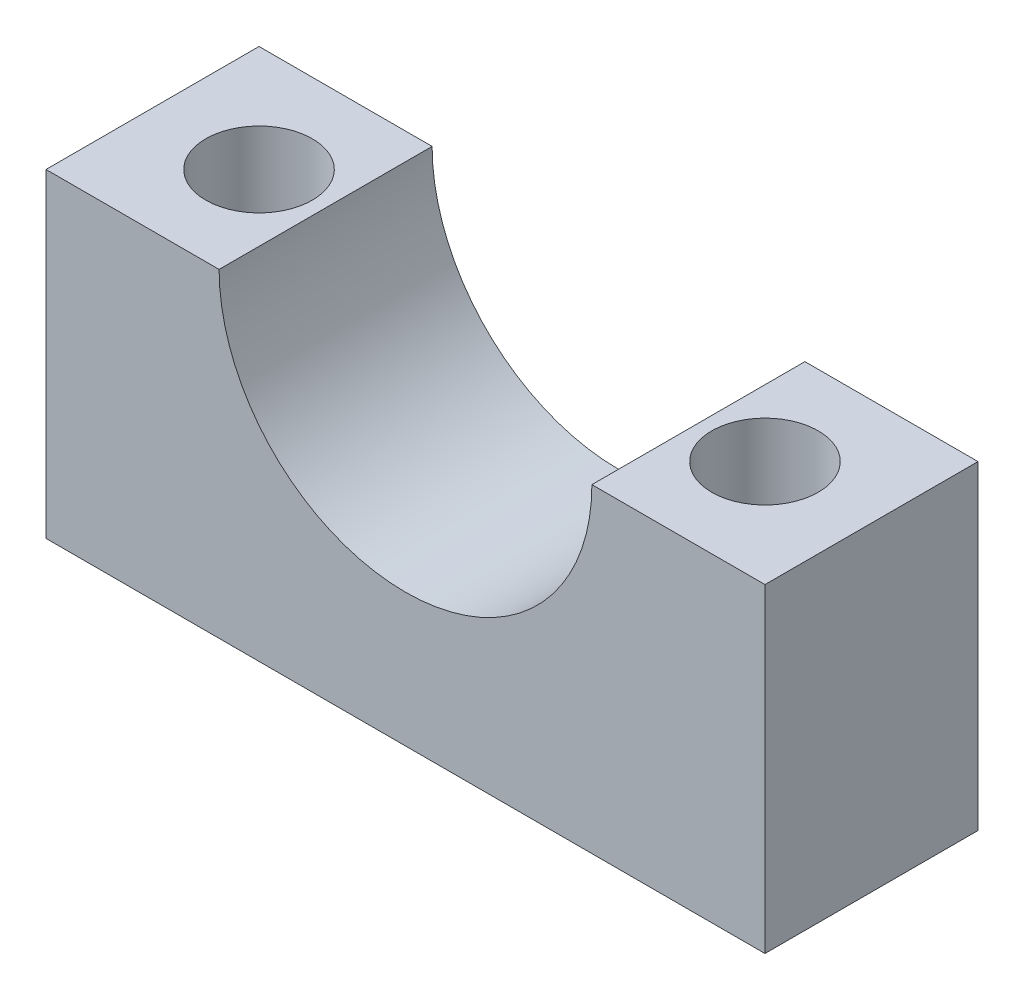
SolidWorks part; units mm, degrees
material "AISI 304"
ref_plane "Front Plane" through (0, 0, 0) normal (0, 0, 1) x (1, 0, 0)
ref_plane "Top Plane" through (0, 0, 0) normal (0, 1, 0) x (1, 0, 0)
ref_plane "Right Plane" through (0, 0, 0) normal (1, 0, 0) x (0, 0, -1)
sketch "Sketch1" plane through (0, 0, 0) normal (0, 0, 1) x (1, 0, 0)
  line L1 (-7.886, -1.9153) -> (19.114, -1.9153)
  line L2 (-7.886, -1.9153) -> (-7.886, 10.0847)
  line L3 (-7.886, 10.0847) -> (19.114, 10.0847)
  line L4 (19.114, -1.9153) -> (19.114, 10.0847)
  circle A0 centre (5.614, 10.0847) radius 7
  dimension "D3" = 14
  dimension "D1" = 12
  dimension "D2" = 27
extrude "Boss-Extrude1" add sketch "Sketch1" along normal blind 8 contours A0 L3 L2 L1 L4
sketch "Sketch2" plane through (0, 10.0847, 0) normal (0, 1, 0) x (1, 0, 0)
  line L0 (19.114, -8) -> (19.114, 0) construction
  line L1 (-7.886, 0) -> (-1.386, 0) construction
  line L2 (12.614, 0) -> (19.114, 0) construction
  circle A0 centre (-3.886, -4) radius 2
  circle A1 centre (15.114, -4) radius 2
  dimension "D2" = 4
  dimension "D3" = 4
  dimension "D1" = 19
  dimension "D4" = 4
  dimension "D5" = 4
  dimension "D6" = 4
extrude "Cut-Extrude1" cut sketch "Sketch2" against normal through all
